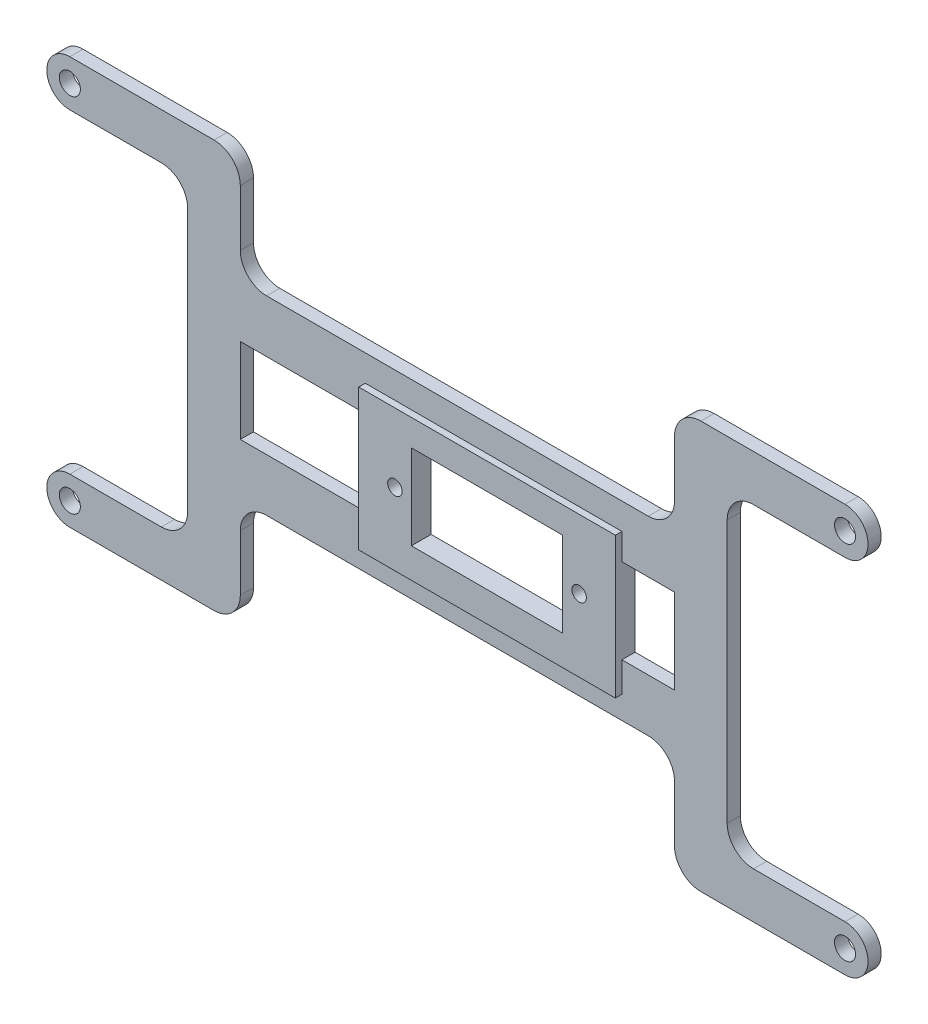
SolidWorks part; units mm, degrees
ref_plane "Front Plane" through (0, 0, 0) normal (0, 0, 1) x (1, 0, 0)
ref_plane "Top Plane" through (0, 0, 0) normal (0, 1, 0) x (1, 0, 0)
ref_plane "Right Plane" through (0, 0, 0) normal (1, 0, 0) x (0, 0, -1)
sketch "Sketch1" plane through (0, 0, 0) normal (0, 0, 1) x (1, 0, 0)
  line L1 (0, 0) -> (0, 3.5)
  line L4 (0, 0) -> (0, 54.9422)
  line L5 (0, 3.5) -> (37.9119, 3.5)
  line L6 (79.9119, 40.9711) -> (79.9119, 13.9711)
  line L7 (0, 51.4422) -> (37.9119, 51.4422)
  line L9 (45.9119, 51.4422) -> (45.9119, 58.4422)
  line L10 (117.8238, 58.4422) -> (71.9119, 58.4422)
  line L11 (66.9119, 5.9711) -> (71.9119, 5.9711)
  line L12 (71.9119, 5.9711) -> (71.9119, 3.5)
  line L13 (117.8238, -3.5) -> (71.9119, -3.5)
  line L15 (66.9119, 40.9711) -> (50.9119, 40.9711)
  line L17 (66.9119, 48.9711) -> (50.9119, 48.9711)
  line L18 (66.9119, 13.9711) -> (50.9119, 13.9711)
  line L19 (66.9119, 5.9711) -> (50.9119, 5.9711)
  line L22 (71.9119, 27.4711) -> (71.9119, 40.9711)
  line L23 (66.9119, 13.9711) -> (71.9119, 13.9711)
  line L24 (79.9119, 13.9711) -> (79.9119, 3.5)
  line L25 (71.9119, 3.5) -> (71.9119, -3.5)
  line L26 (79.9119, 3.5) -> (117.8238, 3.5)
  line L27 (71.9119, 27.4711) -> (71.9119, 13.9711)
  line L28 (50.9119, 5.9711) -> (45.9119, 5.9711)
  line L29 (45.9119, 5.9711) -> (45.9119, 3.5)
  line L30 (50.9119, 13.9711) -> (45.9119, 13.9711)
  line L31 (37.9119, 13.9711) -> (37.9119, 3.5)
  line L32 (79.9119, 40.9711) -> (79.9119, 51.4422)
  line L33 (66.9119, 40.9711) -> (71.9119, 40.9711)
  line L34 (66.9119, 48.9711) -> (71.9119, 48.9711)
  line L35 (71.9119, 48.9711) -> (71.9119, 51.4422)
  line L36 (50.9119, 48.9711) -> (45.9119, 48.9711)
  line L37 (45.9119, 48.9711) -> (45.9119, 51.4422)
  line L38 (37.9119, 40.9711) -> (37.9119, 51.4422)
  line L39 (50.9119, 40.9711) -> (45.9119, 40.9711)
  line L41 (45.9119, 3.5) -> (45.9119, -3.5)
  line L42 (45.9119, -3.5) -> (0, -3.5)
  line L43 (71.9119, 51.4422) -> (71.9119, 58.4422)
  line L44 (45.9119, 58.4422) -> (0, 58.4422)
  line L45 (79.9119, 51.4422) -> (117.8238, 51.4422)
  line L46 (37.9119, 40.9711) -> (37.9119, 13.9711)
  line L48 (45.9119, 27.4711) -> (45.9119, 40.9711)
  line L49 (45.9119, 27.4711) -> (45.9119, 13.9711)
  circle A0 centre (0, 54.9422) radius 1.6
  circle A1 centre (117.8238, 54.9422) radius 1.6
  circle A2 centre (117.8238, 0) radius 1.6
  circle A3 centre (0, 0) radius 1.6
  arc A4 (0, 58.4422) -> (0, 51.4422) centre (0, 54.9422) ccw
  arc A5 (117.8238, 51.4422) -> (117.8238, 58.4422) centre (117.8238, 54.9422) ccw
  arc A6 (117.8238, -3.5) -> (117.8238, 3.5) centre (117.8238, 0) ccw
  arc A7 (0, 3.5) -> (0, -3.5) centre (0, 0) ccw
  circle A8 centre (66.9119, 44.9711) radius 2.1
  circle A9 centre (66.9119, 9.9711) radius 2.1
  circle A14 centre (50.9119, 9.9711) radius 2.1
  circle A15 centre (50.9119, 44.9711) radius 2.1
  point P32 (58.9119, 40.9711)
  point P34 (58.9119, 48.9711)
  point P36 (58.9119, 13.9711)
  point P41 (58.9119, 5.9711)
  dimension "D1" = 54.9422
  dimension "D2" = 3.5
  dimension "D3" = 117.8238
extrude "Boss-Extrude3" add sketch "Sketch1" along normal blind 2
sketch "Sketch3" plane through (0, 0, 2) normal (0, 0, 1) x (1, 0, 0)
  line L0 (71.9119, 13.9711) -> (99.9119, 13.9711)
  line L1 (99.9119, 13.9711) -> (99.9119, 3.5)
  line L2 (79.9119, 3.5) -> (117.8238, 3.5) construction
  line L3 (71.9119, 13.9711) -> (71.9119, 5.9711)
  line L4 (71.9119, 5.9711) -> (91.9119, 5.9711)
  line L5 (91.9119, 5.9711) -> (91.9119, 3.5)
  line L6 (91.9119, 3.5) -> (99.9119, 3.5)
  line L12 (91.9119, 51.4422) -> (99.9119, 51.4422)
  line L13 (91.9119, 48.9711) -> (91.9119, 51.4422)
  line L14 (71.9119, 48.9711) -> (91.9119, 48.9711)
  line L15 (71.9119, 40.9711) -> (71.9119, 48.9711)
  line L16 (99.9119, 40.9711) -> (99.9119, 51.4422)
  line L17 (71.9119, 40.9711) -> (99.9119, 40.9711)
  line L18 (45.9119, 40.9711) -> (17.9119, 40.9711)
  line L19 (17.9119, 40.9711) -> (17.9119, 51.4422)
  line L20 (45.9119, 40.9711) -> (45.9119, 48.9711)
  line L21 (45.9119, 48.9711) -> (25.9119, 48.9711)
  line L22 (25.9119, 48.9711) -> (25.9119, 51.4422)
  line L23 (25.9119, 51.4422) -> (17.9119, 51.4422)
  line L24 (25.9119, 3.5) -> (17.9119, 3.5)
  line L25 (25.9119, 5.9711) -> (25.9119, 3.5)
  line L26 (45.9119, 5.9711) -> (25.9119, 5.9711)
  line L27 (45.9119, 13.9711) -> (45.9119, 5.9711)
  line L28 (17.9119, 13.9711) -> (17.9119, 3.5)
  line L29 (45.9119, 13.9711) -> (17.9119, 13.9711)
extrude "Boss-Extrude4" add sketch "Sketch3" against normal up to surface (2 mm away) up to face at (58.9119, 27.4711, 0)
sketch "Sketch4" plane through (0, 0, 2) normal (0, 0, 1) x (1, 0, 0)
  line L0 (25.9119, 48.9711) -> (25.9119, 65.3112)
  line L1 (25.9119, 48.9711) -> (91.9119, 48.9711)
  line L2 (91.9119, 48.9711) -> (91.9119, 65.3112)
  line L3 (91.9119, 65.3112) -> (25.9119, 65.3112)
  line L4 (25.9119, 5.9711) -> (91.9119, 5.9711)
  line L5 (91.9119, 5.9711) -> (91.9119, -18.7705)
  line L6 (91.9119, -18.7705) -> (25.9119, -18.7705)
  line L7 (25.9119, -18.7705) -> (25.9119, 5.9711)
extrude "Cut-Extrude3" cut sketch "Sketch4" against normal blind 14.5
fillet "Fillet1" radius 4 16 edges at (25.9119, 48.9711, 1) (25.9119, 58.4422, 1) (17.9119, 51.4422, 1) (17.9119, 40.9711, 1) (25.9119, 5.9711, 1) (25.9119, -3.5, 1) (17.9119, 3.5, 1) (17.9119, 13.9711, 1) (99.9119, 13.9711, 1) (99.9119, 3.5, 1) (91.9119, 5.9711, 1) (91.9119, -3.5, 1) (99.9119, 40.9711, 1) (99.9119, 51.4422, 1) (91.9119, 48.9711, 1) (91.9119, 58.4422, 1)
sketch "Sketch5" plane through (0, 0, 2) normal (0, 0, 1) x (1, 0, 0)
  line L0 (45.9119, 40.9711) -> (45.9119, 13.9711)
  line L3 (45.9119, 13.9711) -> (71.9119, 13.9711)
  line L5 (71.9119, 13.9711) -> (71.9119, 40.9711)
  line L6 (71.9119, 40.9711) -> (45.9119, 40.9711)
  circle A0 centre (58.9119, 27.4711) radius 6
extrude "Boss-Extrude5" add sketch "Sketch5" against normal up to surface (2 mm away) up to face at (58.9119, 27.4711, 0)
sketch "Sketch6" plane through (0, 0, 2) normal (0, 0, 1) x (1, 0, 0)
  line L0 (37.9119, 40.9711) -> (42.9119, 40.9711)
  line L1 (37.9119, 13.9711) -> (42.9119, 13.9711)
  line L2 (42.9119, 13.9711) -> (42.9119, 40.9711)
  line L3 (37.9119, 40.9711) -> (37.9119, 13.9711)
  line L4 (79.9119, 13.9711) -> (74.9119, 13.9711)
  line L5 (74.9119, 13.9711) -> (74.9119, 40.9711)
  line L6 (74.9119, 40.9711) -> (79.9119, 40.9711)
  line L7 (79.9119, 40.9711) -> (79.9119, 13.9711)
extrude "Cut-Extrude4" cut sketch "Sketch6" against normal blind 14.5
sketch "Sketch7" plane through (0, 0, 2) normal (0, 0, 1) x (1, 0, 0)
  line L1 (80.8919, 27.4711) -> (80.8919, 40.9711)
  line L2 (74.9119, 40.9711) -> (95.9119, 40.9711) construction
  line L3 (88.8919, 27.4711) -> (88.8919, 40.9711)
  line L4 (80.8919, 27.4711) -> (80.8919, 13.9711)
  line L5 (95.9119, 13.9711) -> (74.9119, 13.9711) construction
  line L6 (80.8919, 13.9711) -> (88.8919, 13.9711)
  line L7 (88.8919, 13.9711) -> (88.8919, 27.4711)
  line L8 (88.8919, 40.9711) -> (80.8919, 40.9711)
  circle A1 centre (84.8919, 27.4711) radius 2.5
extrude "Boss-Extrude6" add sketch "Sketch7" against normal up to surface (2 mm away) up to face at (1.6, 0, 0)
sketch "Sketch8" plane through (0, 0, 2) normal (0, 0, 1) x (1, 0, 0)
  circle A0 centre (48.8309, 27.4711) radius 2.5
extrude "Cut-Extrude5" cut sketch "Sketch8" against normal blind 10
sketch "Sketch9" plane through (0, 0, 2) normal (0, 0, 1) x (1, 0, 0)
  line L1 (42.9119, 40.9711) -> (44.8309, 40.9711)
  line L2 (74.9119, 40.9711) -> (74.9119, 13.9711)
  line L3 (74.9119, 13.9711) -> (52.8309, 13.9711)
  line L4 (42.9119, 13.9711) -> (42.9119, 40.9711)
  line L5 (44.8309, 27.4711) -> (44.8309, 40.9711)
  line L8 (52.8309, 40.9711) -> (52.8309, 13.9711)
  line L10 (44.8309, 27.4711) -> (44.8309, 13.9711)
  line L11 (52.8309, 40.9711) -> (74.9119, 40.9711)
  line L12 (44.8309, 13.9711) -> (42.9119, 13.9711)
extrude "Cut-Extrude6" cut sketch "Sketch9" against normal blind 10
sketch "Sketch10" plane through (0, 0, 2) normal (0, 0, 1) x (1, 0, 0)
  line L2 (44.8309, 13.9711) -> (44.8309, 40.9711) construction
  line L5 (44.8309, 13.9711) -> (44.8309, 13.0211)
  line L6 (44.8309, 13.0211) -> (88.8919, 13.0211)
  line L7 (88.8919, 13.9711) -> (88.8919, 40.9711) construction
  line L8 (88.8919, 13.0211) -> (88.8919, 13.9711)
  line L9 (88.8919, 40.9711) -> (88.8919, 41.9211)
  line L10 (88.8919, 41.9211) -> (44.8309, 41.9211)
  line L11 (44.8309, 41.9211) -> (44.8309, 40.9711)
  line L12 (44.8309, 40.9711) -> (12.9645, 40.9711)
  line L13 (12.9645, 40.9711) -> (12.9645, 51.4422)
  line L14 (0, 51.4422) -> (13.9119, 51.4422) construction
  line L15 (12.9645, 51.4422) -> (106.0206, 51.4422)
  line L16 (103.9119, 51.4422) -> (117.8238, 51.4422) construction
  line L17 (106.0206, 51.4422) -> (106.0206, 40.9711)
  line L18 (106.0206, 40.9711) -> (88.8919, 40.9711)
  line L19 (44.8309, 13.9711) -> (12.9645, 13.9711)
  line L20 (12.9645, 13.9711) -> (12.9645, 3.5)
  line L22 (106.0206, 3.5) -> (106.0206, 13.9711)
  line L23 (106.0206, 13.9711) -> (88.8919, 13.9711)
  line L26 (12.9645, 3.5) -> (106.0206, 3.5)
extrude "Cut-Extrude7" cut sketch "Sketch10" against normal blind 10
sketch "Sketch11" plane through (0, 0, 2) normal (0, 0, 1) x (1, 0, 0)
  line L1 (52.8309, 33.9211) -> (80.8919, 33.9211)
  line L2 (80.8919, 40.9711) -> (80.8919, 13.9711) construction
  line L3 (80.8919, 33.9211) -> (80.8919, 40.9711)
  line L4 (80.8919, 40.9711) -> (52.8309, 40.9711)
  line L5 (52.8309, 40.9711) -> (52.8309, 33.9211)
  line L6 (52.8309, 40.9711) -> (52.8309, 13.9711) construction
  line L8 (52.8309, 21.0211) -> (80.8919, 21.0211)
  line L9 (80.8919, 21.0211) -> (80.8919, 13.9711)
  line L10 (80.8919, 13.9711) -> (52.8309, 13.9711)
  line L11 (52.8309, 13.9711) -> (52.8309, 21.0211)
extrude "Boss-Extrude7" add sketch "Sketch11" against normal up to surface (2 mm away) up to face at (66.8614, 27.4711, 0)
sketch "Sketch12" plane through (0, 0, 2) normal (0, 0, 1) x (1, 0, 0)
  line L0 (25.9119, 1.2355) -> (25.9119, 54.4422)
  line L1 (25.9119, 0.5) -> (25.9119, 1.9711) construction
  line L2 (25.9119, 54.4422) -> (91.9119, 54.4422)
  line L3 (91.9119, 54.4422) -> (91.9119, 0.5)
  line L4 (91.9119, 0.5) -> (25.9119, 1.2355)
  line L5 (44.8309, 41.9211) -> (44.8309, 13.0211)
  line L6 (44.8309, 13.0211) -> (88.8919, 13.0211)
  line L7 (88.8919, 13.0211) -> (88.8919, 41.9211)
  line L8 (88.8919, 41.9211) -> (44.8309, 41.9211)
extrude "Cut-Extrude9" cut sketch "Sketch12" against normal blind 10
sketch "Sketch13" plane through (0, 0, 2) normal (0, 0, 1) x (1, 0, 0)
  line L0 (25.9119, 3.5) -> (25.9119, 13.0211)
  line L1 (44.8309, 13.0211) -> (25.9119, 13.0211)
  line L2 (25.9119, 41.9211) -> (25.9119, 51.4422)
  line L3 (17.9119, 13.0211) -> (17.9119, 3.5)
  line L4 (0, 3.5) -> (25.9119, 3.5) construction
  line L5 (17.9119, 13.0211) -> (17.9119, 51.4422)
  line L6 (0, 51.4422) -> (25.9119, 51.4422) construction
  line L7 (91.9119, 51.4422) -> (91.9119, 41.9211)
  line L8 (88.8919, 41.9211) -> (91.9119, 41.9211)
  line L9 (91.9119, 33.9211) -> (88.8919, 33.9211)
  line L10 (99.9119, 41.9211) -> (99.9119, 51.4422)
  line L11 (91.9119, 51.4422) -> (117.8238, 51.4422) construction
  line L12 (99.9119, 51.4422) -> (99.9119, 3.5)
  line L13 (91.9119, 3.5) -> (117.8238, 3.5) construction
  line L14 (88.8919, 13.0211) -> (88.8919, 41.9211) construction
  line L15 (88.8919, 13.0211) -> (91.9119, 13.0211)
  line L16 (88.8919, 33.9211) -> (88.8919, 41.9211)
  line L17 (91.9119, 21.0211) -> (88.8919, 21.0211)
  line L18 (44.8309, 41.9211) -> (25.9119, 41.9211)
  line L19 (91.9119, 33.9211) -> (91.9119, 21.0211)
  line L20 (44.8309, 33.9211) -> (25.9119, 33.9211)
  line L21 (91.9119, 13.0211) -> (91.9119, 3.5)
  line L22 (44.8309, 21.0211) -> (25.9119, 21.0211)
  line L23 (88.8919, 21.0211) -> (88.8919, 13.0211)
  line L24 (44.8309, 13.0211) -> (44.8309, 21.0211)
  line L25 (44.8309, 33.9211) -> (44.8309, 41.9211)
  line L26 (17.9119, 51.4422) -> (25.9119, 51.4422)
  line L27 (25.9119, 3.5) -> (17.9119, 3.5)
  line L28 (91.9119, 3.5) -> (99.9119, 3.5)
  line L29 (91.9119, 51.4422) -> (99.9119, 51.4422)
  line L30 (25.9119, 21.0211) -> (25.9119, 33.9211)
  line M3 (25.9119, 3.5) -> (0, 3.5)
extrude "Boss-Extrude9" add sketch "Sketch13" against normal blind 2 contours L22 L30 L20 L25 L18 L2 L26 L5 L3 L0 L1 L24 M3 | L29 L7 L8 L16 L9 L19 L17 L23 L15 L21 L28 L12 L10
fillet "Fillet2" radius 4 8 edges at (17.9119, 3.5, 1) (17.9119, 51.4422, 1) (25.9119, 41.9211, 1) (25.9119, 13.0211, 1) (91.9119, 13.0211, 1) (91.9119, 41.9211, 1) (99.9119, 3.5, 1) (99.9119, 51.4422, 1)
sketch "Sketch14" plane through (0, 0, 2) normal (0, 0, 1) x (1, 0, 0)
  line L0 (44.8309, 33.9211) -> (44.8309, 37.9211)
  line L2 (88.8919, 33.9211) -> (88.8919, 37.9211)
  line L3 (88.8919, 37.9211) -> (44.8309, 37.9211)
  line L4 (44.8309, 33.9211) -> (44.8309, 21.0211)
  line L5 (44.8309, 21.0211) -> (44.8309, 16.4792)
  line L6 (44.8309, 16.4792) -> (88.8919, 16.4792)
  line L7 (88.8919, 16.4792) -> (88.8919, 21.0211)
  line L8 (88.8919, 21.0211) -> (88.8919, 33.9211)
  line L9 (80.8919, 21.0211) -> (80.8919, 33.9211)
  line L10 (80.8919, 33.9211) -> (52.8309, 33.9211)
  line L11 (52.8309, 33.9211) -> (52.8309, 21.0211)
  line L12 (52.8309, 21.0211) -> (80.8919, 21.0211)
  circle A0 centre (48.8309, 27.4711) radius 2.5
  circle A1 centre (84.8919, 27.4711) radius 2.5
extrude "Boss-Extrude10" add sketch "Sketch14" along normal blind 1
sketch "Sketch15" plane through (52.8309, 0, 0) normal (1, 0, 0) x (0, 0, -1)
  line L0 (0, 33.9211) -> (-3, 33.9211)
  line L1 (-3, 33.9211) -> (-3, 21.0211)
  line L2 (-3, 21.0211) -> (0, 21.0211)
  line L3 (0, 21.0211) -> (-3, 21.0211) construction
  line L4 (0, 33.9211) -> (0, 21.0211) construction
  line L5 (0, 21.0211) -> (0, 33.9211)
extrude "Boss-Extrude11" add sketch "Sketch15" along normal blind 2.5
sketch "Sketch16" plane through (80.8919, 0, 0) normal (-1, 0, 0) x (0, 0, 1)
  line L0 (0, 33.9211) -> (3, 33.9211)
  line L1 (3, 33.9211) -> (3, 21.0211)
  line L2 (3, 21.0211) -> (0, 21.0211)
  line L3 (0, 21.0211) -> (0, 33.9211)
extrude "Boss-Extrude12" add sketch "Sketch16" along normal blind 2.5
sketch "Sketch17" plane through (0, 0, 3) normal (0, 0, 1) x (1, 0, 0)
  line L0 (58.9119, 33.9211) -> (58.9119, 21.0211)
  line L5 (58.9119, 33.9211) -> (52.9119, 33.9211)
  line L7 (58.9119, 21.0211) -> (52.9119, 21.0211)
  line L8 (55.3309, 21.0211) -> (78.3919, 21.0211) construction
  line L9 (52.9119, 21.0211) -> (52.9119, 33.9211)
extrude "Cut-Extrude12" cut sketch "Sketch17" against normal blind 5.5
sketch "Sketch19" plane through (0, 0, 3) normal (0, 0, 1) x (1, 0, 0)
  line L3 (75.9119, 27.4711) -> (75.9119, 33.9211)
  line L4 (78.3919, 33.9211) -> (52.9119, 33.9211) construction
  line L5 (75.9119, 33.9211) -> (78.3919, 33.9211)
  line L6 (78.3919, 33.9211) -> (78.3919, 21.0211)
  line L7 (78.3919, 21.0211) -> (75.9119, 21.0211)
  line L8 (52.9119, 21.0211) -> (78.3919, 21.0211) construction
  line L9 (75.9119, 21.0211) -> (75.9119, 27.4711)
extrude "Boss-Extrude13" add sketch "Sketch19" against normal up to surface (3 mm away) up to face at (65.6519, 27.4711, 0)
sketch "Sketch20" plane through (0, 0, 3) normal (0, 0, 1) x (1, 0, 0)
  line L4 (83.9119, 27.4711) -> (83.9119, 37.9211)
  line L5 (88.8919, 37.9211) -> (44.8309, 37.9211) construction
  line L6 (44.9119, 27.4711) -> (44.9119, 37.9211)
  line L7 (44.9119, 37.9211) -> (83.9119, 37.9211)
  line L8 (44.9119, 27.4711) -> (44.9119, 16.4792)
  line L9 (44.8309, 16.4792) -> (88.8919, 16.4792) construction
  line L10 (44.9119, 16.4792) -> (83.9119, 16.4792)
  line L11 (83.9119, 16.4792) -> (83.9119, 27.4711)
  line L12 (37.5032, 44.9732) -> (36.0401, -4.5973)
  line L13 (36.0401, -4.5973) -> (97.14, -2.2563)
  line L14 (97.14, -2.2563) -> (103.8704, 35.7263)
  line L15 (103.8704, 35.7263) -> (82.9185, 46.9045)
  line L16 (82.9185, 46.9045) -> (37.5032, 44.9732)
extrude "Cut-Extrude13" cut sketch "Sketch20" against normal up to surface (1 mm away) up to face at (119.4238, 0, 2)
sketch "Sketch21" plane through (0, 0, 2) normal (0, 0, 1) x (1, 0, 0)
  line L0 (44.8309, 21.0211) -> (44.9119, 21.0211)
  line L1 (44.9119, 16.4792) -> (44.9119, 37.9211) construction
  line L2 (44.8309, 33.9211) -> (44.9119, 33.9211)
  line L3 (44.9119, 37.9211) -> (44.9119, 16.4792) construction
  line L4 (44.9119, 33.9211) -> (44.9119, 21.0211)
  line L5 (44.8309, 21.0211) -> (44.8309, 33.9211)
  line L6 (88.8919, 33.9211) -> (83.9119, 33.9211)
  line L7 (83.9119, 37.9211) -> (83.9119, 29.771) construction
  line L8 (88.8919, 33.9211) -> (88.8919, 21.0211)
  line L9 (88.8919, 21.0211) -> (83.9119, 21.0211)
  line L10 (83.9119, 16.4792) -> (83.9119, 25.1712) construction
  line L11 (83.9119, 21.0211) -> (83.9119, 33.9211)
extrude "Cut-Extrude14" cut sketch "Sketch21" against normal blind 5.5
sketch "Sketch22" plane through (0, 0, 3) normal (0, 0, 1) x (1, 0, 0)
  line L0 (83.9119, 25.1712) -> (83.9119, 29.771)
  line L1 (83.9119, 29.771) -> (78.2921, 33.2922)
  line L2 (78.2921, 33.2922) -> (79.1814, 24.0861)
  line L3 (79.1814, 24.0861) -> (83.9119, 25.1712)
  circle A0 centre (48.8309, 27.4711) radius 2.5
extrude "Boss-Extrude14" add sketch "Sketch22" against normal up to surface (3 mm away) up to face at (64.4119, 27.4711, 0)
sketch "Sketch23" plane through (0, 0, 2) normal (0, 0, 1) x (1, 0, 0)
  circle A0 centre (50.4119, 27.4711) radius 1.1
  circle A1 centre (78.4119, 27.4711) radius 1.1
extrude "Cut-Extrude17" cut sketch "Sketch23" against normal blind 5.5 and the other way blind 5.5
